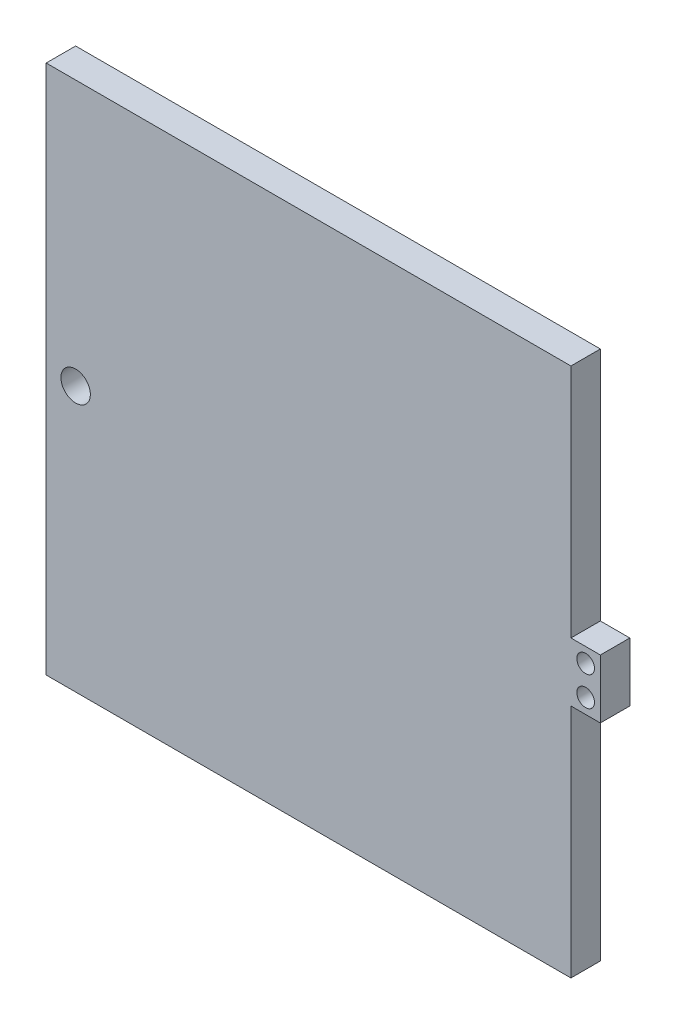
SolidWorks part; units mm, degrees
material "PET"
ref_plane "Front Plane" through (0, 0, 0) normal (0, 0, 1) x (1, 0, 0)
ref_plane "Top Plane" through (0, 0, 0) normal (0, 1, 0) x (1, 0, 0)
ref_plane "Right Plane" through (0, 0, 0) normal (1, 0, 0) x (0, 0, -1)
sketch "Sketch2" plane through (0, 0, 0) normal (0, 0, 1) x (1, 0, 0)
  line L1 (-122.4216, 87.1773) -> (103.8924, 87.1773)
  line L2 (-122.4216, 87.1773) -> (-122.4216, -128.7227)
  line L3 (-122.4216, -128.7227) -> (103.8924, -128.7227)
  line L4 (103.8924, 87.1773) -> (103.8924, -128.7227)
  dimension "D1" = 215.9
  dimension "D2" = 226.314
extrude "Boss-Extrude1" add sketch "Sketch2" along normal blind 12.7
sketch "Sketch3" plane through (103.8924, 0, 0) normal (1, 0, 0) x (0, 0, -1)
  line L0 (-12.7, -128.7227) -> (-12.7, 87.1773) construction
  line L1 (-12.7, -1.7227) -> (0, -1.7227)
  line L2 (-12.7, -1.7227) -> (-12.7, -27.1227)
  line L3 (-12.7, -27.1227) -> (0, -27.1227)
  line L4 (0, -1.7227) -> (0, -27.1227)
  line L5 (0, -128.7227) -> (0, 87.1773) construction
  point P8 (0, -14.4227)
  dimension "D1" = 25.4
  dimension "D2" = 101.6
extrude "Boss-Extrude2" add sketch "Sketch3" along normal blind 12.7
sketch "Sketch4" plane through (0, 0, 0) normal (0, 0, -1) x (-1, 0, 0)
  line L1 (-103.8924, 87.1773) -> (122.4216, 87.1773) construction
  line L6 (122.4216, 87.1773) -> (122.4216, -128.7227) construction
  line L7 (-116.5924, -27.1227) -> (-116.5924, -1.7227) construction
  line L8 (-116.5924, -1.7227) -> (-103.8924, -1.7227) construction
  circle A0 centre (109.7216, -14.4227) radius 6.35
  circle A1 centre (-110.2424, -8.0727) radius 3.81
  circle A3 centre (-110.2424, -20.7727) radius 3.81
  dimension "D1" = 12.7
  dimension "D4" = 6.35
  dimension "D2" = 101.6
  dimension "D3" = 12.7
  dimension "D5" = 6.35
  dimension "D6" = 2
extrude "Cut-Extrude1" cut sketch "Sketch4" against normal blind 12.7
sketch "Sketch5" plane through (0, 87.1773, 0) normal (0, 1, 0) x (1, 0, 0)
  line L1 (-122.4216, 0) -> (103.8924, 0)
  line L2 (-122.4216, 0) -> (-122.4216, -12.7)
  line L3 (-122.4216, -12.7) -> (103.8924, -12.7)
  line L4 (103.8924, 0) -> (103.8924, -12.7)
extrude "Boss-Extrude3" add sketch "Sketch5" along normal blind 12.7
